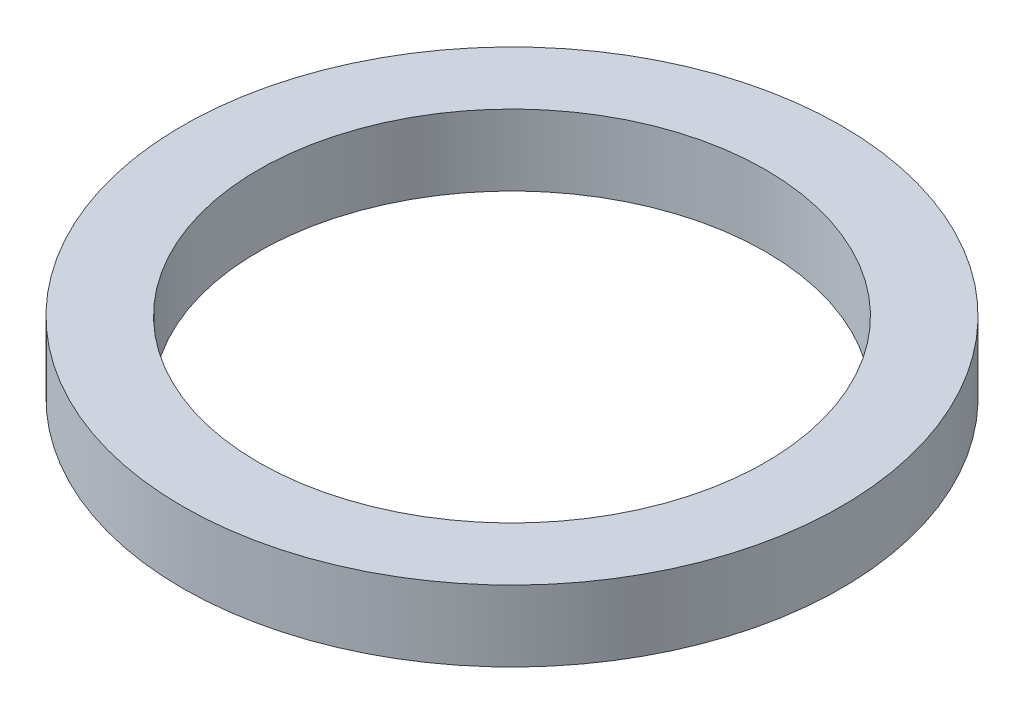
SolidWorks part; units mm, degrees
ref_plane "Front Plane" through (0, 0, 0) normal (0, 0, 1) x (1, 0, 0)
ref_plane "Top Plane" through (0, 0, 0) normal (0, 1, 0) x (1, 0, 0)
ref_plane "Right Plane" through (0, 0, 0) normal (1, 0, 0) x (0, 0, -1)
other "Bounding Box"
ref_plane "Default Plane" through (-8.9266, -12.7485, 0) normal (-0.1736, 0.9848, 0) x (0.9848, 0.1736, 0)
sketch "Sketch1" plane through (0, 0, 0) normal (0, 1, 0) x (1, 0, 0)
  circle A0 centre (0, 0) radius 25
  circle A1 centre (0, 0) radius 32.5
  dimension "D1" = 50
  dimension "D2" = 65
extrude "Boss-Extrude1" add sketch "Sketch1" along normal mid plane 7
